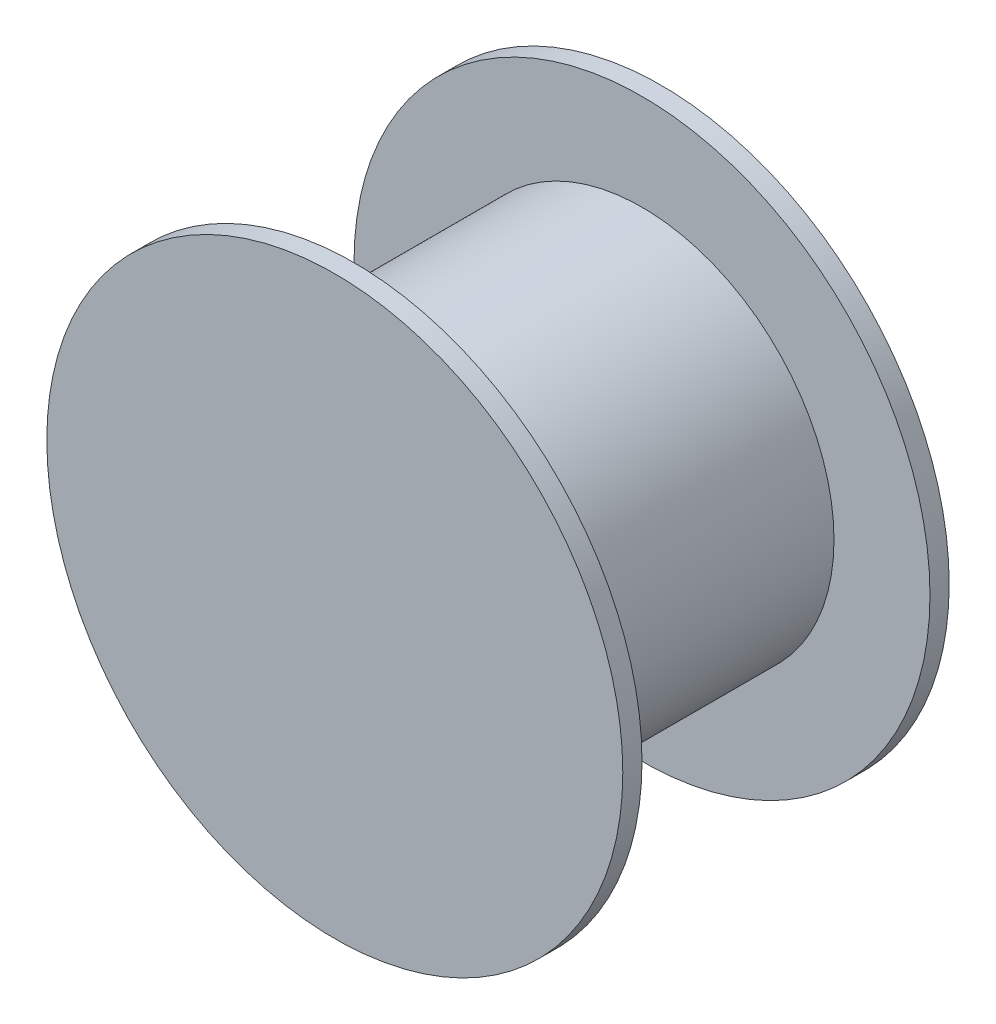
SolidWorks part; units mm, degrees
ref_plane "Front Plane" through (0, 0, 0) normal (0, 0, 1) x (1, 0, 0)
ref_plane "Top Plane" through (0, 0, 0) normal (0, 1, 0) x (1, 0, 0)
ref_plane "Right Plane" through (0, 0, 0) normal (1, 0, 0) x (0, 0, -1)
sketch "Sketch1" plane through (0, 0, 0) normal (0, 0, 1) x (1, 0, 0)
  circle A0 centre (0, 0) radius 10
  dimension "D1" = 20
extrude "Boss-Extrude1" add sketch "Sketch1" along normal blind 16
sketch "Sketch2" plane through (0, 0, 16) normal (0, 0, 1) x (1, 0, 0)
  circle A0 centre (0, 0) radius 15
extrude "Boss-Extrude2" add sketch "Sketch2" against normal blind 1
ref_plane "Plane1" through (0, 0, 7.5) normal (0, 0, -1) x (-1, 0, 0)
mirror "Mirror1" about plane through (0, 0, 7.5) normal (0, 0, -1) of "Boss-Extrude2"
scale "Scale1" scale about centroid uniform scaling yes scale factor 0.2
scale "Scale2" scale about centroid uniform scaling yes scale factor 2
